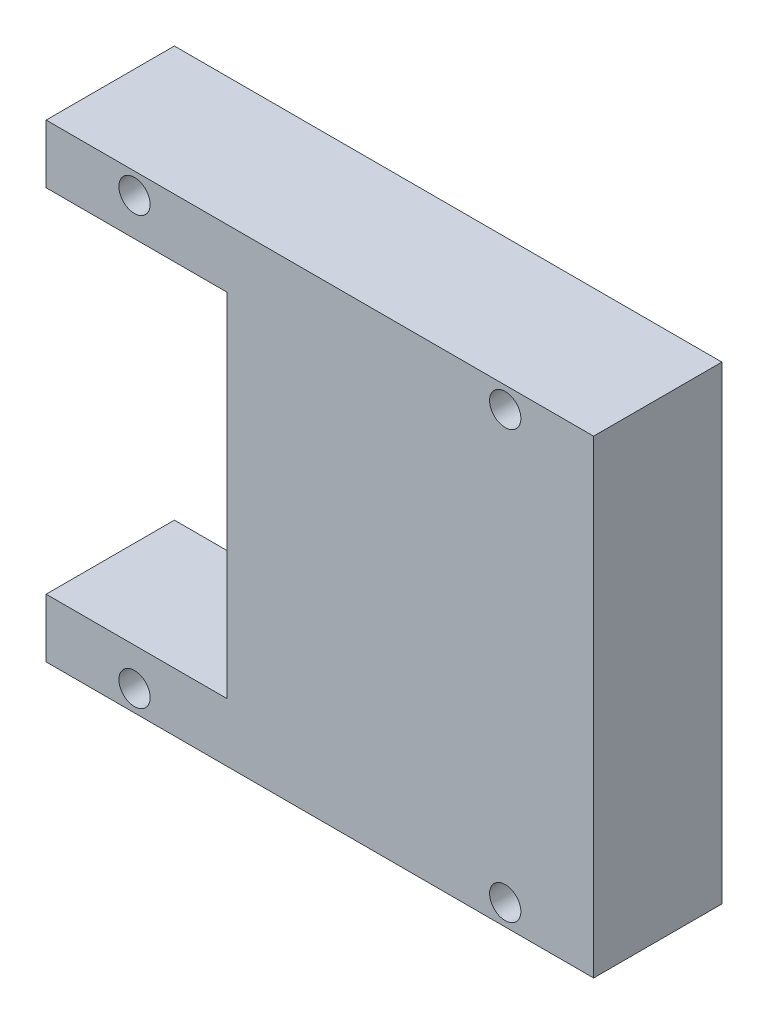
SolidWorks part; units mm, degrees
ref_plane "Front Plane" through (0, 0, 0) normal (0, 0, 1) x (1, 0, 0)
ref_plane "Top Plane" through (0, 0, 0) normal (0, 1, 0) x (1, 0, 0)
ref_plane "Right Plane" through (0, 0, 0) normal (1, 0, 0) x (0, 0, -1)
sketch "Sketch3" plane through (0, 0, 0) normal (0, 0, 1) x (1, 0, 0)
  line L0 (-121.55, -15) -> (-156.55, -15)
  line L1 (-121.55, -15) -> (-121.55, 15)
  line L2 (-156.55, -15) -> (-156.55, -11.25)
  line L3 (-121.55, 15) -> (-156.55, 15)
  line L4 (-156.55, -11.25) -> (-156.55, -15.95) construction
  line L5 (-139.05, -15) -> (-139.05, 15) construction
  line L6 (-145, -11.25) -> (-156.55, -11.25)
  line L7 (-145, -11.25) -> (-145, 11.25)
  line L9 (-145, 11.25) -> (-156.55, 11.25)
  line L10 (-156.55, 11.25) -> (-145.25, 11.25) construction
  line L11 (-150.9, -11.25) -> (-145.25, -11.25) construction
  line L12 (-145, -15) -> (145, -15) construction
  line L13 (-156.55, 11.25) -> (-156.55, 15)
  line L14 (-145, 15) -> (-145, -15) construction
  circle A0 centre (-150.9, 13.65) radius 1
  circle A1 centre (-150.9, -13.65) radius 1
  arc A2 (-150.575, -14.5957) -> (-151.225, -14.5957) centre (-150.9, -13.65) ccw construction
  arc A3 (-151.225, 14.5957) -> (-150.575, 14.5957) centre (-150.9, 13.65) ccw construction
  circle A4 centre (-127.2, 13.65) radius 1
  circle A5 centre (-127.2, -13.65) radius 1
  dimension "D1" = 30
  dimension "D2" = 35
extrude "Boss-Extrude1" add sketch "Sketch3" along normal blind 8.2
